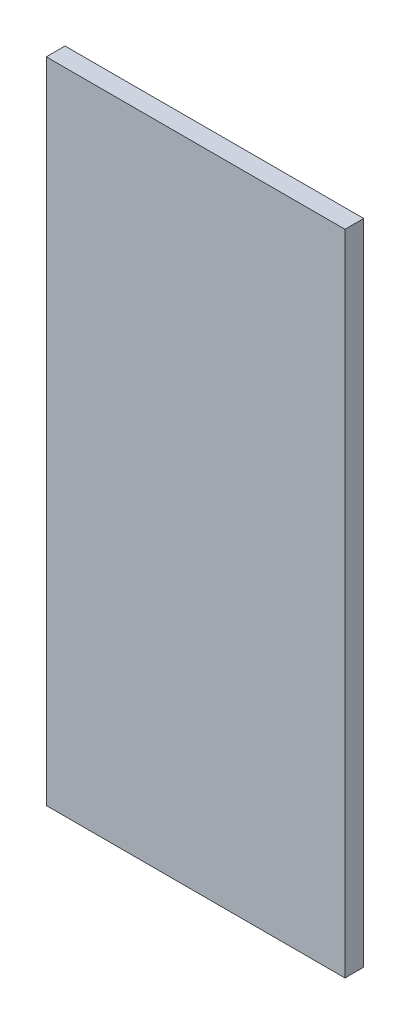
SolidWorks part; units mm, degrees
ref_plane "Front Plane" through (0, 0, 0) normal (0, 0, 1) x (1, 0, 0)
ref_plane "Top Plane" through (0, 0, 0) normal (0, 1, 0) x (1, 0, 0)
ref_plane "Right Plane" through (0, 0, 0) normal (1, 0, 0) x (0, 0, -1)
sketch "Sketch1" plane through (0, 0, 0) normal (0, 0, 1) x (1, 0, 0)
  line L1 (143.5, -311.5) -> (-143.5, -311.5)
  line L2 (143.5, -311.5) -> (143.5, 311.5)
  line L3 (143.5, 311.5) -> (-143.5, 311.5)
  line L4 (-143.5, -311.5) -> (-143.5, 311.5)
  line L5 (143.5, -311.5) -> (-143.5, 311.5) construction
  line L6 (143.5, 311.5) -> (-143.5, -311.5) construction
  point P0 (0, 0)
  dimension "D1" = 623
  dimension "D2" = 287
extrude "Boss-Extrude1" add sketch "Sketch1" along normal blind 18
equation "\"H_DSP\"=18"
equation "\"D1@Boss-Extrude1\"=\"H_DSP\""
